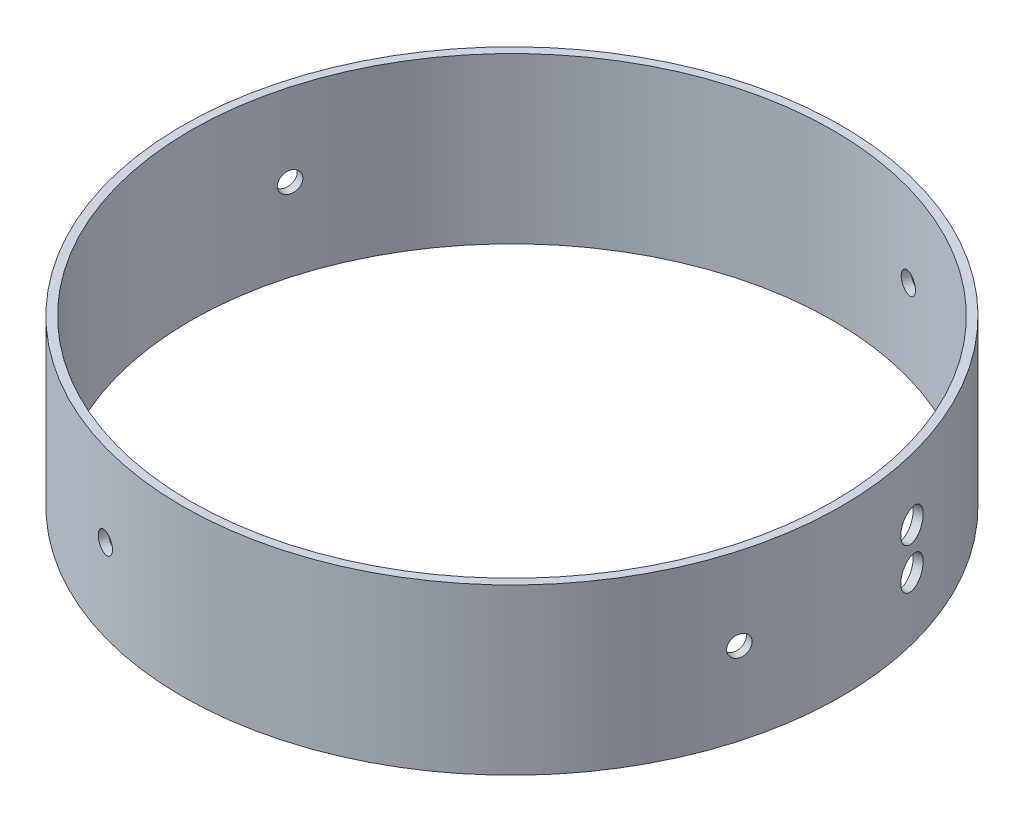
SolidWorks part; units mm, degrees
material "Wildman Fiberglass"
ref_plane "Front Plane" through (0, 0, 0) normal (0, 0, 1) x (1, 0, 0)
ref_plane "Top Plane" through (0, 0, 0) normal (0, 1, 0) x (1, 0, 0)
ref_plane "Right Plane" through (0, 0, 0) normal (1, 0, 0) x (0, 0, -1)
sketch "Sketch1" plane through (0, 0, 0) normal (0, 1, 0) x (1, 0, 0)
  circle A0 centre (0, 0) radius 49.53
  circle A1 centre (0, 0) radius 50.8
  dimension "D1" = 101.6
  dimension "D2" = 99.06
extrude "Boss-Extrude1" add sketch "Sketch1" along normal blind 25.4
extrude "Cut-Extrude1" cut sketch "Sketch2" against normal blind 25.4
sketch "Sketch2" plane through (80.7093, 206.3332, 111.646) normal (0.9693, 0, -0.2457) x (0, -1, 0)
  circle A0 centre (196.8082, 128.0554) radius 2.3813
  circle A1 centre (190.4582, 128.0554) radius 2.3813
  point P3 (0, 0)
  point P6 (0, 0)
  point P8 (0, 0)
extrude "Cut-Extrude2" cut sketch "Sketch3" against normal blind 37.338
sketch "Sketch3" plane through (-3.1003, 207.7782, 134.799) normal (-0.9623, 0, -0.2719) x (0, 1, 0)
  circle A0 centre (-195.0782, 130.5648) radius 1.5875
  point P2 (0, 0)
  point P3 (-80.7782, 130.5648)
  point P4 (-195.0782, 181.3648)
pattern_circular "CirPattern1" count 4 over 360 of "Cut-Extrude2"
equation "\"Length\"=1"
equation "\"D1@Boss-Extrude1\"=\"Length\""
